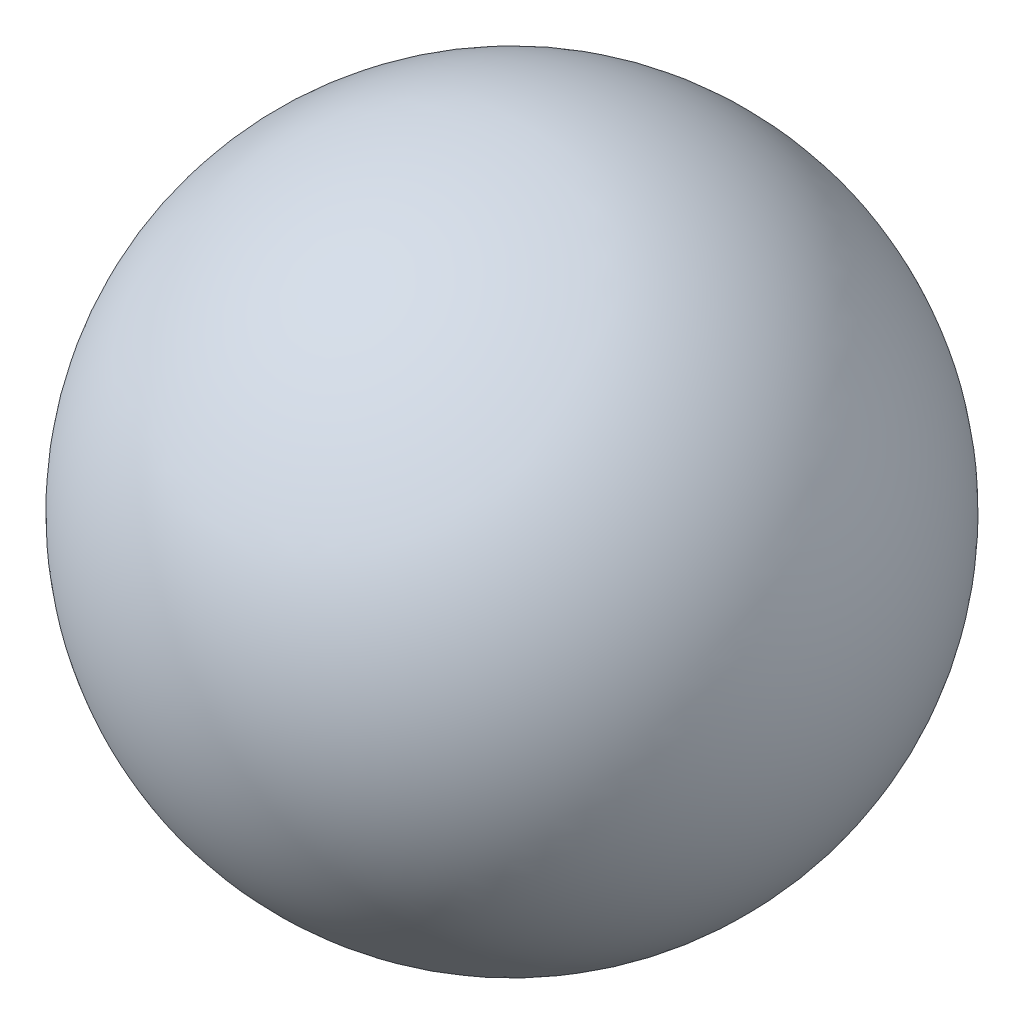
SolidWorks part; units mm, degrees
ref_plane "Front" through (0, 0, 0) normal (0, 0, 1) x (1, 0, 0)
ref_plane "Top" through (0, 0, 0) normal (0, 1, 0) x (1, 0, 0)
ref_plane "Right" through (0, 0, 0) normal (1, 0, 0) x (0, 0, -1)
sketch "Sketch1" plane through (0, 0, 0) normal (0, 1, 0) x (1, 0, 0)
  line L0 (0, 0.25) -> (0, -0.25)
  line L1 (0, 0.3713) -> (0, -0.3857) construction
  arc A0 (0, -0.25) -> (0, 0.25) centre (0, 0) ccw
  dimension "D1" = 0.5
revolve "Revolve1" add sketch "Sketch1" angle 360 about L1
